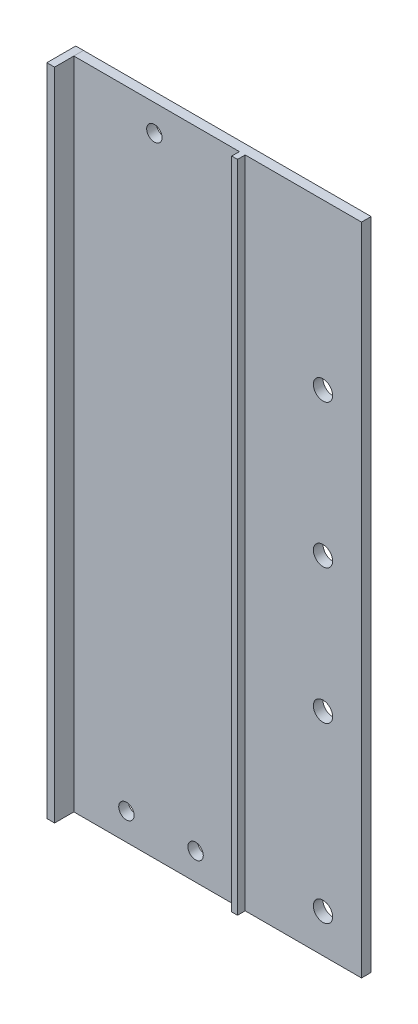
SolidWorks part; units mm, degrees
ref_plane "Front Plane" through (0, 0, 0) normal (0, 0, 1) x (1, 0, 0)
ref_plane "Top Plane" through (0, 0, 0) normal (0, 1, 0) x (1, 0, 0)
ref_plane "Right Plane" through (0, 0, 0) normal (1, 0, 0) x (0, 0, -1)
sketch "Sketch1" plane through (0, 0, 0) normal (0, 0, 1) x (1, 0, 0)
  line L1 (0, 0) -> (74.7, 0)
  line L2 (0, 0) -> (0, 170)
  line L3 (0, 170) -> (74.7, 170)
  line L4 (74.7, 0) -> (74.7, 170)
  circle A0 centre (20.9139, 163.0937) radius 2
  circle A1 centre (31.6133, 7.0213) radius 2
  circle A2 centre (13.6516, 7.0213) radius 2
  point P11 (0, 0)
  point P12 (0, 0)
extrude "Boss-Extrude1" add sketch "Sketch1" along normal blind 2.5
sketch "Sketch2" plane through (0, 0, 2.5) normal (0, 0, 1) x (1, 0, 0)
  line L1 (0, 170) -> (-2, 170)
  line L2 (0, 170) -> (0, 0)
  line L3 (0, 0) -> (-2, 0)
  line L4 (-2, 170) -> (-2, 0)
extrude "Boss-Extrude2" add sketch "Sketch2" along normal blind 7.5 from surface at -2.5 separate body starting at face at (33.6133, 7.0213, 0)
sketch "Sketch3" plane through (0, 0, 0) normal (0, 0, -1) x (-1, 0, 0)
  circle A1 centre (-64.7, 10) radius 2.5
  circle A2 centre (-64.7, 55) radius 2.5
  circle A3 centre (-64.7, 90) radius 2.5
extrude "Cut-Extrude1" cut sketch "Sketch3" against normal blind 5
sketch "Sketch4" plane through (0, 0, 2.5) normal (0, 0, 1) x (1, 0, 0)
  line L0 (0, 170) -> (43, 170)
  line L1 (74.7, 170) -> (0, 170) construction
  line L2 (0, 0) -> (74.7, 0) construction
  line L3 (43, 170) -> (44.5, 170)
  line L4 (43, 170) -> (43, 0)
  line L5 (43, 0) -> (44.5, 0)
  line L6 (44.5, 170) -> (44.5, 0)
extrude "Boss-Extrude3" add sketch "Sketch4" along normal blind 2 contours L4 L5 L6 L3
sketch "Sketch5" plane through (0, 0, 2.5) normal (0, 0, 1) x (1, 0, 0)
  circle A0 centre (64.7, 127.25) radius 2.5
extrude "Cut-Extrude2" cut sketch "Sketch5" against normal blind 12
